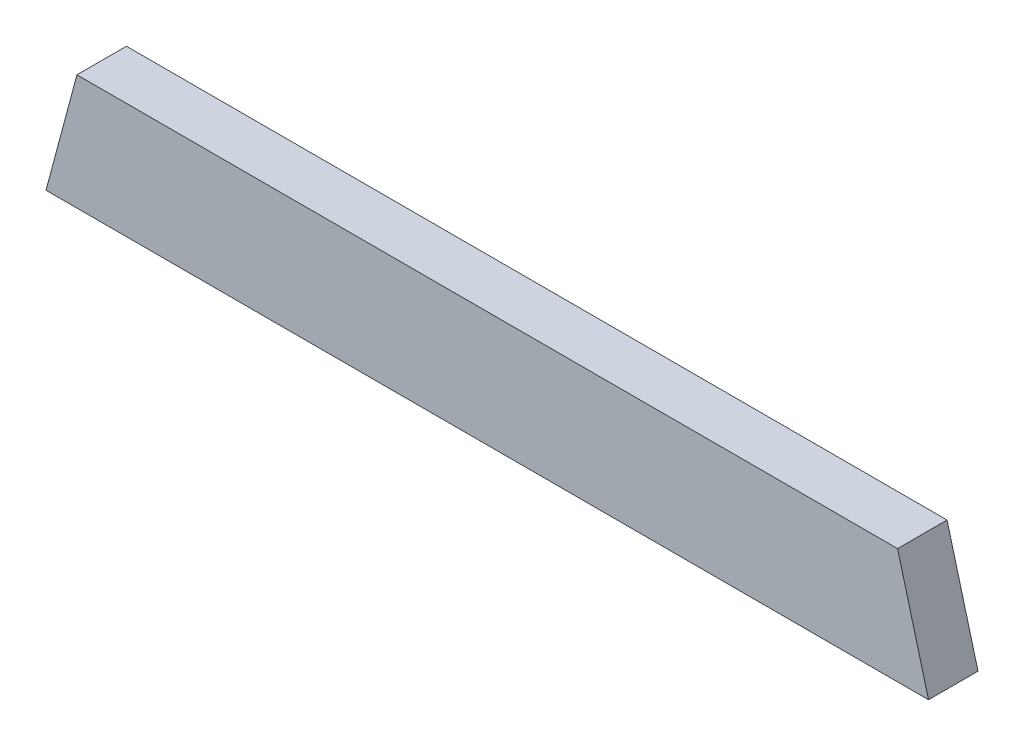
SolidWorks part; units mm, degrees
ref_plane "Front Plane" through (0, 0, 0) normal (0, 0, 1) x (1, 0, 0)
ref_plane "Top Plane" through (0, 0, 0) normal (0, 1, 0) x (1, 0, 0)
ref_plane "Right Plane" through (0, 0, 0) normal (1, 0, 0) x (0, 0, -1)
sketch "Sketch1" plane through (0, 0, 0) normal (0, 0, 1) x (1, 0, 0)
  line L0 (-315.9125, 88.9) -> (-339.7332, 0)
  line L1 (-339.7332, 0) -> (339.7332, 0)
  line L2 (339.7332, 0) -> (315.9125, 88.9)
  line L3 (315.9125, 88.9) -> (-315.9125, 88.9)
  dimension "D1" = 631.825
  dimension "D2" = 88.9
  dimension "D3" = 30
extrude "Boss-Extrude1" add sketch "Sketch1" along normal blind 38.1
